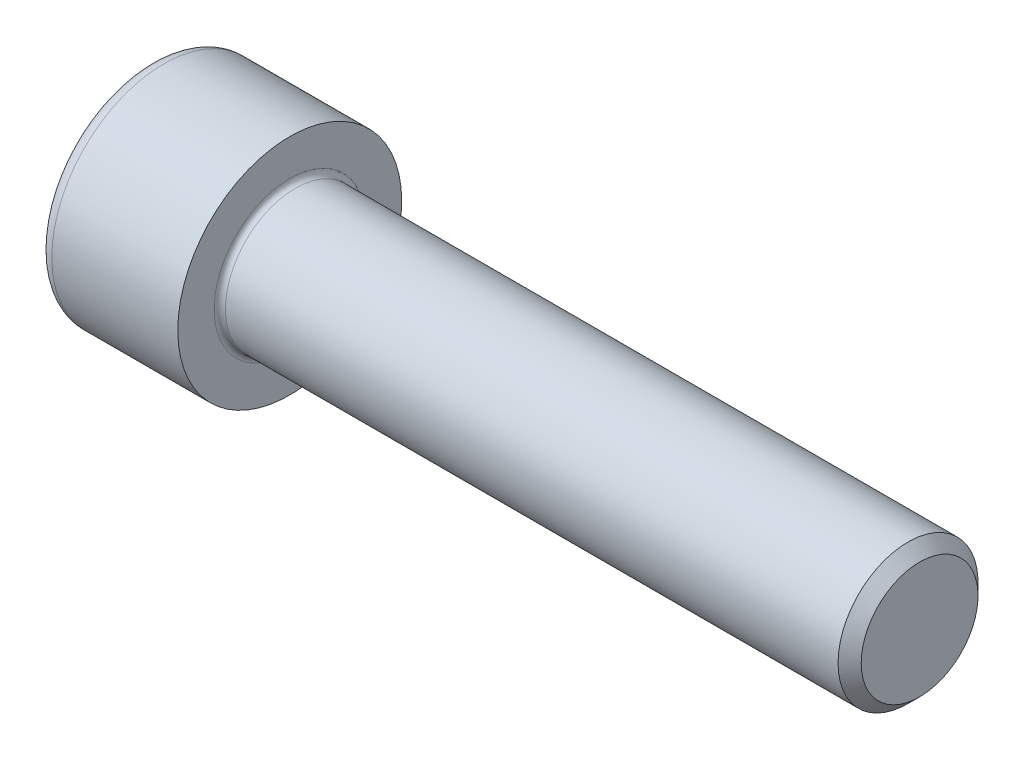
SolidWorks part; units mm, degrees
revolve "Base-Revolve" add sketch "BodySke"
sketch "BodySke" plane through (0, 0, 0) normal (0, 0, 1) x (1, 0, 0)
  line L0 (0, 0) -> (0, 8)
  line L1 (0, 8) -> (10, 8)
  line L2 (10, 8) -> (10, 5)
  line L3 (10, 5) -> (54.172, 5)
  line L4 (55, 4.172) -> (55, 0)
  line L5 (55, 0) -> (0, 0)
  line L6 (-31.75, 0) -> (127, 0) construction
  line L8 (55, 4.172) -> (54.172, 5)
  line L10 (55, -4.172) -> (54.172, -5) construction
  line L11 (11.5, 9.525) -> (11.5, 3.175) construction
  line L12 (23, 9.525) -> (23, 3.175) construction
  line L13 (-5, 9.525) -> (-5, 3.175) construction
  dimension "Length" = 45
  dimension "Body_ch_ang" = 45
  dimension "Thread_length" = 60
cosmetic thread "ThreadCosmetic" [suppressed]
fillet "Fillet1" radius 0.4 1 edges at (10, 0, 5)
fillet "Fillet2" radius 1 1 edges at (0, 0, 8)
ref_plane "Plane1" through (0, 0, 0) normal (0, 0, 1) x (1, 0, 0)
ref_plane "Plane2" through (0, 0, 0) normal (0, 1, 0) x (1, 0, 0)
ref_plane "Plane3" through (0, 0, 0) normal (1, 0, 0) x (0, 0, -1)
sketch "Sketch2" plane through (0, 0, 0) normal (0, 0, 1) x (1, 0, 0)
  line L0 (0, 4.0125) -> (5, 4.0125)
  line L1 (5, 4.0125) -> (7.3166, 0)
  line L2 (-31.75, 0) -> (127, 0) construction
  line L3 (7.3166, 0) -> (0, 0)
  line L4 (0, 0) -> (0, 4.0125)
  line L6 (0, 0) -> (47.625, 0) construction
  dimension "D2" = 60
revolve "Hex-PreBroach" cut sketch "Sketch2" angle 360 about L6
sketch "Sketch3" plane through (0, 0, 0) normal (-1, 0, 0) x (0, 0.5, 0.866)
  line L0 (2.3166, 4.0125) -> (-2.3166, 4.0125)
  line L1 (-2.3166, 4.0125) -> (-4.6332, 0)
  line L2 (2.3166, 4.0125) -> (4.6332, 0)
  line L3 (2.3166, -4.0125) -> (4.6332, 0)
  line L4 (2.3166, -4.0125) -> (-2.3166, -4.0125)
  line L5 (-2.3166, -4.0125) -> (-4.6332, 0)
extrude "Hex" cut sketch "Sketch3" against normal blind 5
sketch "ThdSchSke" plane through (0, 0, 0) normal (0, 0, 1) x (1, 0, 0)
  line L0 (23, -4.172) -> (22.4202, -5)
  line L1 (23, -4.172) -> (23.5798, -5)
  line L2 (23.5798, -5) -> (23.5798, -6.25)
  line L3 (-3.175, 0) -> (5.1513, 0) construction
  line L4 (0, 7) -> (0, -7) construction
  line L5 (23.5798, -6.25) -> (22.4202, -6.25)
  line L6 (22.4202, -6.25) -> (22.4202, -5)
revolve "ThreadSchematic" [suppressed] cut sketch "ThdSchSke" angle 360 about L3
pattern_linear "ThdSchPat" [suppressed]
equation "\"D2@Sketch3\" = \"Hex_size@Sketch3\" / 2"
equation "\"D1@Sketch3\" = \"Hex_size@Sketch3\" / 2"
equation "\"D1@Sketch2\" = \"Hex_size@Sketch3\" / 2"
equation "\"Thread_minor@ThreadCosmetic\"  =  \"Minor_dia@BodySke\""
equation "\"Depth@Sketch2\" =  \"Key_eng@Hex\""
equation "\"Thread_length@ThreadCosmetic\" = ((sgn( (\"Length@BodySke\" - \"Advance@BodySke\" * 3.0) - \"Thread_nom@BodySke\" )-1)*( (\"Length@BodySke\" - \"Advance@BodySke\" * 3.0) - \"Thread_nom@BodySke\" ))/-2+ \"Thread_nom@BodySke\""
equation "\"Thread_minor@ThdSchSke\" = \"Minor_dia@BodySke\""
equation "\"Diameter@ThdSchSke\" = \"Diameter@BodySke\""
equation "\"Overcut@ThdSchSke\" = \"Diameter@BodySke\" * 1.25"
equation "\"Start@ThdSchSke\" = \"Head_ht@BodySke\" + \"Length@BodySke\" - \"Thread_length@ThreadCosmetic\"  '---Non-countersunk---"
equation "\"Num_threads@ThdSchPat\" = int( \"Thread_length@ThreadCosmetic\" / \"Advance@BodySke\" + 0.999 )  + 1"
equation "\"Advance@ThdSchPat\" = \"Thread_length@ThreadCosmetic\" /  (\"Num_threads@ThdSchPat\" - 1) 'relax it"
equation "\"Num_threads@ThdSchPat\" = \"Num_threads@ThdSchPat\" - sgn( \"Num_threads@ThdSchPat\" - 1) '---chamfered tips only---"
